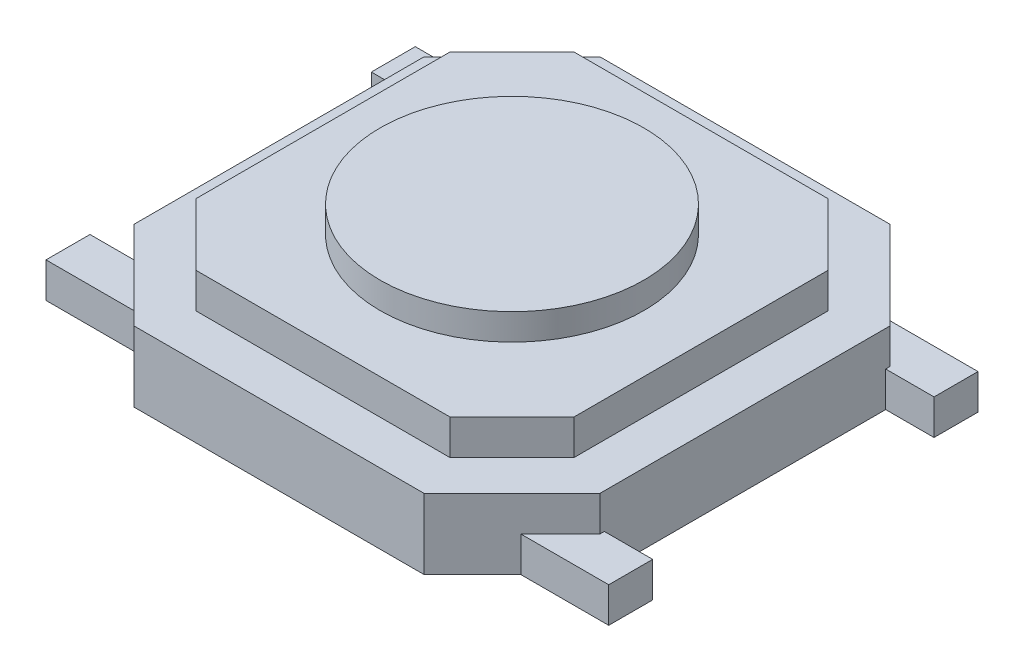
SolidWorks part; units mm, degrees
ref_plane "Front" through (0, 0, 0) normal (0, 0, 1) x (1, 0, 0)
ref_plane "Top" through (0, 0, 0) normal (0, 1, 0) x (1, 0, 0)
ref_plane "Right" through (0, 0, 0) normal (1, 0, 0) x (0, 0, -1)
sketch "Sketch1" plane through (0, 0, 0) normal (0, 1, 0) x (1, 0, 0)
  line L0 (0, 0) -> (3.1929, 0) construction
  line L1 (0, 0) -> (0, 4.2) construction
  line L2 (-3.2, 2.1) -> (3.2, 2.1)
  line L3 (3.2, 2.1) -> (3.2, 1.6)
  line L4 (-3.2, 1.6) -> (-2.2, 1.6)
  line L5 (3.2, -2.1) -> (3.2, -1.6)
  line L6 (-3.2, -2.1) -> (3.2, -2.1)
  line L7 (-3.2, -2.1) -> (-3.2, -1.6)
  line L8 (-3.2, -1.6) -> (-2.2, -1.6)
  line L9 (-3.2, 2.1) -> (-3.2, 1.6)
  line L10 (-2.2, 1.6) -> (-2.2, -1.6)
  line L11 (3.2, -1.6) -> (2.2, -1.6)
  line L12 (2.2, 1.6) -> (2.2, -1.6)
  line L13 (3.2, 1.6) -> (2.2, 1.6)
  point P8 (-3.2, 0)
  point P10 (-2.2, 0)
  point P11 (3.2, 0)
  point P22 (0, -2.1)
  point P23 (0, 2.1)
  dimension "D1" = 0.5
  dimension "D3" = 4.4
  dimension "D2" = 4.2
  dimension "D4" = 6.4
extrude "Extrude1" add sketch "Sketch1" along normal blind 0.4
sketch "Sketch2" plane through (0, 0, 0) normal (0, 1, 0) x (-1, 0, 0)
  line L0 (1.65, -2.65) -> (2.65, -1.65)
  line L2 (-2.65, -1.65) -> (-1.65, -2.65)
  line L4 (-2.65, 1.65) -> (-2.65, -1.65)
  line L5 (-1.65, -2.65) -> (1.65, -2.65)
  line L6 (-1.65, 2.65) -> (1.65, 2.65)
  line L7 (2.65, 1.65) -> (2.65, -1.65)
  line L8 (-2.65, 1.65) -> (-1.65, 2.65)
  line L9 (1.65, 2.65) -> (2.65, 1.65)
  line L10 (0, 0) -> (-2.2842, 0) construction
  line L11 (0, 0) -> (0, -1.8326) construction
  point P0 (2.65, -2.65)
  point P1 (2.65, 2.65)
  point P3 (-2.65, 2.65)
  point P10 (2.65, 0)
  point P11 (-2.65, -2.65)
  point P14 (-2.65, 0)
  point P16 (0, -2.65)
  point P23 (0, 2.65)
  dimension "D1" = 1
  dimension "D2" = 5.3
  dimension "D3" = 5.3
  dimension "D4" = 45
  dimension "D5" = 1
  dimension "D6" = 45
  dimension "D7" = 1
  dimension "D8" = 45
  dimension "D9" = 1
  dimension "D10" = 45
extrude "Extrude2" add sketch "Sketch2" along normal blind 0.8
sketch "Sketch3" plane through (0, 0, 0) normal (0, 1, 0) x (-1, 0, 0)
  line L26 (-2.15, 1.4429) -> (-2.15, -1.4429)
  line L27 (-2.15, -1.4429) -> (-1.4429, -2.15)
  line L28 (-1.4429, -2.15) -> (1.4429, -2.15)
  line L29 (1.4429, -2.15) -> (2.15, -1.4429)
  line L30 (2.15, -1.4429) -> (2.15, 1.4429)
  line L31 (2.15, 1.4429) -> (1.4429, 2.15)
  line L32 (1.4429, 2.15) -> (-1.4429, 2.15)
  line L33 (-1.4429, 2.15) -> (-2.15, 1.4429)
  line L34 (-2.15, 1.4429) -> (-2.15, -1.4429)
  line L35 (-2.15, -1.4429) -> (-1.4429, -2.15)
  line L36 (-1.4429, -2.15) -> (1.4429, -2.15)
  line L37 (1.4429, -2.15) -> (2.15, -1.4429)
  line L38 (2.15, -1.4429) -> (2.15, 1.4429)
  line L39 (2.15, 1.4429) -> (1.4429, 2.15)
  line L40 (1.4429, 2.15) -> (-1.4429, 2.15)
  line L41 (-1.4429, 2.15) -> (-2.15, 1.4429)
  dimension "D1" = 0.5
extrude "Extrude3" add sketch "Sketch3" along normal blind 1.2
sketch "Sketch4" plane through (0, 0, 0) normal (0, 1, 0) x (-1, 0, 0)
  circle A0 centre (0, 0) radius 1.5
  dimension "D1" = 3
extrude "Extrude7" add sketch "Sketch4" along normal blind 1.5
